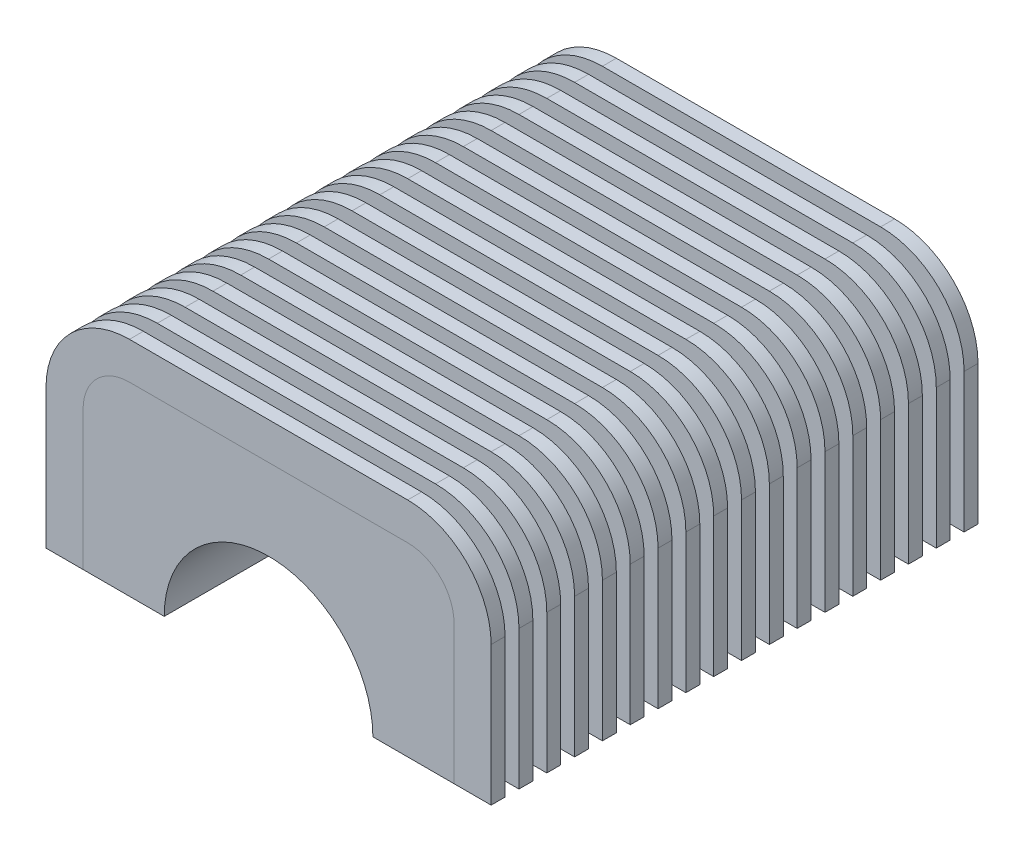
SolidWorks part; units mm, degrees
ref_plane "Płaszczyzna przednia" through (0, 0, 0) normal (0, 0, 1) x (1, 0, 0)
ref_plane "Płaszczyzna górna" through (0, 0, 0) normal (0, 1, 0) x (1, 0, 0)
ref_plane "Płaszczyzna prawa" through (0, 0, 0) normal (1, 0, 0) x (0, 0, -1)
sketch "Szkic2" plane through (0, 0, 0) normal (0, 0, 1) x (1, 0, 0)
  line L0 (0, 0) -> (-40, 0)
  line L13 (-40, 0) -> (-40, 40)
  line L14 (-40, 40) -> (40, 40)
  line L15 (40, 40) -> (40, 0)
  line L16 (40, 0) -> (0, 0)
  circle A0 centre (0, 0) radius 22.5
  dimension "D1" = 45
  dimension "D2" = 40
  dimension "D3" = 80
extrude "Dodanie-wyciągnięcie1" add sketch "Szkic2" against normal blind 108 from offset 0 contours A0 L16 L15 L14 L13 L0
fillet "Zaokrąglenie1" radius 10 1 edges at (-40, 40, -54)
fillet "Zaokrąglenie3" radius 10 1 edges at (40, 40, -54)
sketch "Szkic3" plane through (0, 0, 0) normal (0, 0, 1) x (1, 0, 0)
  line L0 (-40, 0) -> (-48, 0)
  line L1 (40, 0) -> (22.5, 0) construction
  line L2 (40, 0) -> (22.5, 0)
  line L3 (40, 0) -> (48, 0)
  line L12 (40, 30) -> (40, 0) construction
  line L17 (-30, 40) -> (30, 40) construction
  line L18 (-40, 0) -> (-40, 30) construction
  line L19 (40, 30) -> (40, 0)
  line L20 (-30, 40) -> (30, 40)
  line L21 (-40, 0) -> (-40, 30)
  line L22 (-48, 0) -> (-48, 30)
  line L23 (-30, 48) -> (30, 48)
  line L24 (48, 30) -> (48, 0)
  arc A6 (40, 30) -> (30, 40) centre (30, 30) ccw construction
  arc A7 (-30, 40) -> (-40, 30) centre (-30, 30) ccw construction
  arc A12 (40, 30) -> (30, 40) centre (30, 30) ccw
  arc A13 (-30, 40) -> (-40, 30) centre (-30, 30) ccw
  arc A14 (-30, 48) -> (-48, 30) centre (-30, 30) ccw
  arc A15 (48, 30) -> (30, 48) centre (30, 30) ccw
  dimension "D1" = 8
extrude "Dodanie-wyciągnięcie4" add sketch "Szkic3" against normal blind 3 from offset 0 separate body contours L19 A12 L20 A13 L21 L0 L22 A14 L23 A15 L24 L3
pattern_linear "Szyk liniowy4" count 18 spacing 6 along (0, 0, -1) of "Dodanie-wyciągnięcie4"
